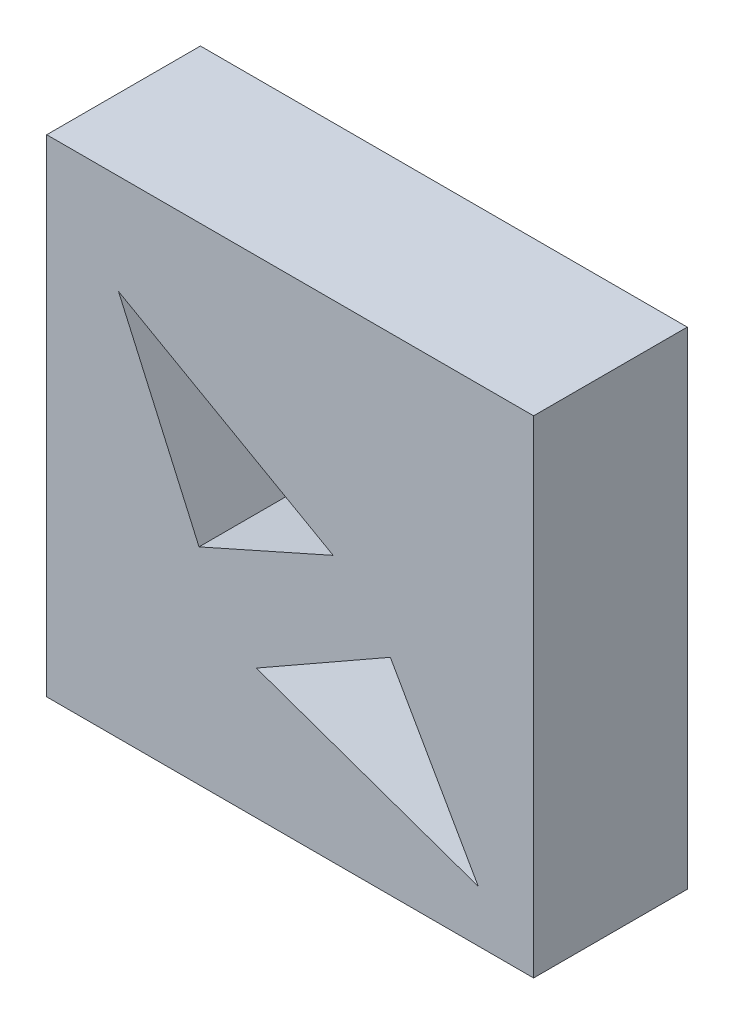
SolidWorks part; units mm, degrees
ref_plane "Plan de face" through (0, 0, 0) normal (0, 0, 1) x (1, 0, 0)
ref_plane "Plan de dessus" through (0, 0, 0) normal (0, 1, 0) x (1, 0, 0)
ref_plane "Plan de droite" through (0, 0, 0) normal (1, 0, 0) x (0, 0, -1)
sketch "Esquisse1" plane through (0, 0, 0) normal (0, 0, 1) x (1, 0, 0)
  line L1 (0, 0) -> (80, 0)
  line L2 (0, 0) -> (0, 80)
  line L3 (0, 80) -> (80, 80)
  line L4 (80, 0) -> (80, 80)
  dimension "D1" = 80
  dimension "D2" = 80
extrude "Boss.-Extru.1" add sketch "Esquisse1" along normal blind 25.25
sketch "Esquisse2" plane through (0, 0, 25.25) normal (0, 0, 1) x (1, 0, 0)
  line L0 (11.7879, 63.6058) -> (25.0268, 33.8645)
  line L1 (25.0268, 33.8645) -> (47.0692, 43.6764)
  line L2 (47.0692, 43.6764) -> (11.7879, 63.6058)
  line L3 (34.4441, 21.3261) -> (56.4604, 33.8645)
  line L4 (56.4604, 33.8645) -> (70.9179, 8.4785)
  line L5 (70.9179, 8.4785) -> (34.4441, 21.3261)
extrude "Enlèv. mat.-Extru.1" cut sketch "Esquisse2" against normal blind 25.25
